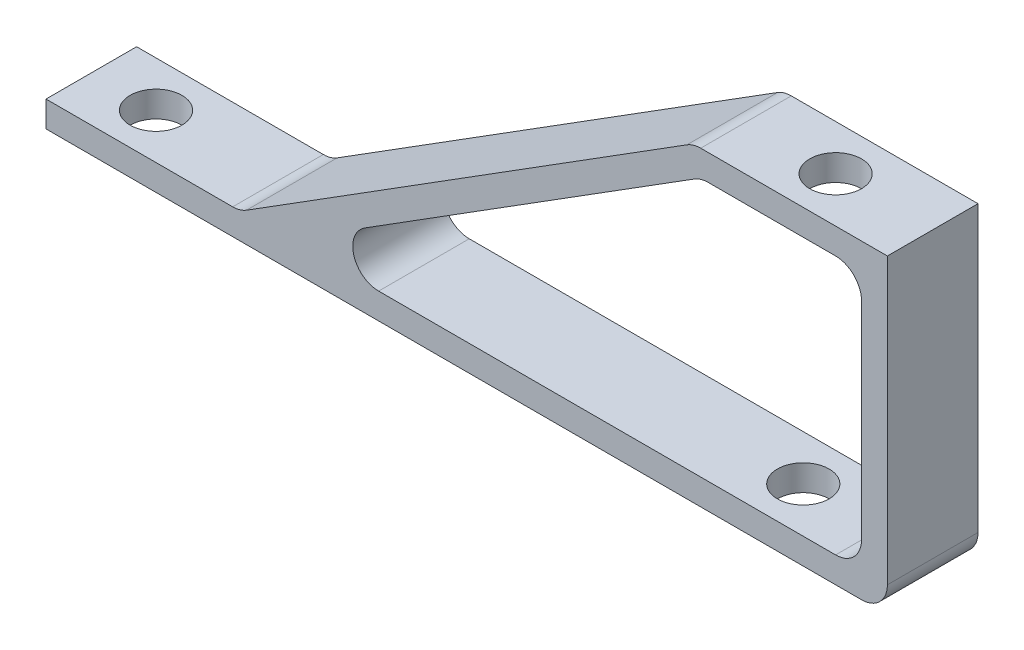
SolidWorks part; units mm, degrees
ref_plane "Front Plane" through (0, 0, 0) normal (0, 0, 1) x (1, 0, 0)
ref_plane "Top Plane" through (0, 0, 0) normal (0, 1, 0) x (1, 0, 0)
ref_plane "Right Plane" through (0, 0, 0) normal (1, 0, 0) x (0, 0, -1)
sketch "Sketch1" plane through (0, 0, 0) normal (0, 1, 0) x (1, 0, 0)
  line L0 (-80.01, -4.445) -> (-73.66, -4.445) construction
  line L1 (0, 0) -> (-80.01, 0)
  line L2 (0, 0) -> (0, -8.89)
  line L3 (0, -8.89) -> (-80.01, -8.89)
  line L4 (-80.01, 0) -> (-80.01, -8.89)
  line L5 (-73.66, -4.445) -> (-10.16, -4.445) construction
  line L6 (-41.91, -4.445) -> (-41.91, -20.2965) construction
  circle A0 centre (-73.66, -4.445) radius 2.54
  circle A1 centre (-10.16, -4.445) radius 2.54
  dimension "D4" = 5.08
  dimension "D1" = 80.01
  dimension "D2" = 8.89
  dimension "D3" = 6.35
  dimension "D5" = 63.5
extrude "Boss-Extrude1" add sketch "Sketch1" along normal blind 2.54
sketch "Sketch2" plane through (0, 0, 0) normal (1, 0, 0) x (0, 0, -1)
  line L1 (-8.89, 0) -> (0, 0)
  line L2 (-8.89, 0) -> (-8.89, 30.48)
  line L3 (-8.89, 30.48) -> (0, 30.48)
  line L4 (0, 0) -> (0, 30.48)
  dimension "D1" = 30.48
  dimension "D2" = 8.89
extrude "Boss-Extrude2" add sketch "Sketch2" along normal blind 2.54
sketch "Sketch3" plane through (0, 30.48, 0) normal (0, 1, 0) x (1, 0, 0)
  line L0 (-80.01, -8.89) -> (0, -8.89) construction
  line L1 (2.54, 0) -> (-16.51, 0)
  line L2 (2.54, 0) -> (2.54, -8.89)
  line L3 (2.54, -8.89) -> (-16.51, -8.89)
  line L4 (-16.51, 0) -> (-16.51, -8.89)
  line L5 (-6.985, 0) -> (-6.985, -8.89) construction
  circle A0 centre (-6.985, -4.445) radius 2.54
  dimension "D2" = 5.08
  dimension "D1" = 19.05
extrude "Boss-Extrude3" add sketch "Sketch3" against normal blind 2.54
sketch "Sketch4" plane through (0, 2.54, 0) normal (0, 1, 0) x (1, 0, 0)
  line L0 (2.54, -4.445) -> (-60.96, -4.445) construction
  line L1 (2.54, 0) -> (2.54, -8.89) construction
  dimension "D1" = 63.5
ref_plane "Plane1" through (-18.4087, 29.2865, 0) normal (-0.5322, 0.8466, 0) x (0.8466, 0.5322, 0)
sketch "Sketch6" plane through (-18.4087, 29.2865, 0) normal (-0.5322, 0.8466, 0) x (0.8466, 0.5322, 0)
  line L0 (-66.3877, -8.89) -> (1.3517, -8.89) construction
  line L1 (2.2426, 0) -> (-50.2592, 0)
  line L2 (2.2426, 0) -> (2.2426, -8.89)
  line L3 (2.2426, -8.89) -> (-50.2592, -8.89)
  line L4 (-50.2592, 0) -> (-50.2592, -8.89)
  dimension "D1" = 52.5019
extrude "Boss-Extrude4" add sketch "Sketch6" against normal blind 2.54
fillet "Fillet1" radius 2.54 7 edges at (2.54, 0, 4.445) (-56.1871, 2.54, 4.445) (0, 2.54, 4.445) (0, 27.94, 4.445) (-15.778, 27.94, 4.445) (-16.51, 30.48, 4.445) (-60.96, 2.54, 4.445)
